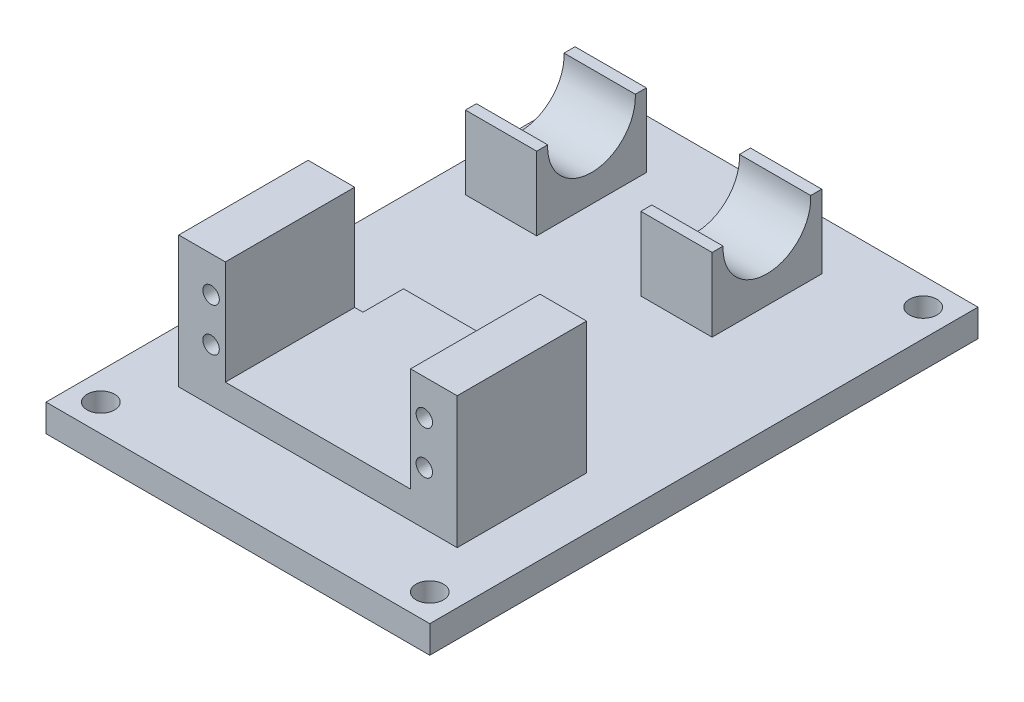
SolidWorks part; units mm, degrees
ref_plane "Front" through (0, 0, 0) normal (0, 0, 1) x (1, 0, 0)
ref_plane "Top" through (0, 0, 0) normal (0, 1, 0) x (1, 0, 0)
ref_plane "Right" through (0, 0, 0) normal (1, 0, 0) x (0, 0, -1)
sketch "Sketch1" plane through (0, 0, 0) normal (0, 1, 0) x (1, 0, 0)
  line L1 (-35, -50) -> (35, -50)
  line L2 (-35, -50) -> (-35, 50)
  line L3 (-35, 50) -> (35, 50)
  line L4 (35, -50) -> (35, 50)
  line L5 (-35, -50) -> (35, 50) construction
  line L6 (-35, 50) -> (35, -50) construction
  point P0 (0, 0)
  dimension "D1" = 70
  dimension "D2" = 100
extrude "Boss-Extrude1" add sketch "Sketch1" along normal blind 5
sketch "Sketch2" plane through (0, 5, 0) normal (0, 1, 0) x (1, 0, 0)
  line L0 (0, 49.7148) -> (0, -60.7462) construction
  line L1 (-15.2897, -11.9) -> (-25.2897, -11.9)
  line L2 (-35, 31) -> (35, 31) construction
  line L3 (-7, 50) -> (-7, -50) construction
  line L4 (-15.2897, -4.5) -> (15.5, -4.5)
  line L5 (-35, -50) -> (35, -50) construction
  line L6 (-35, 50) -> (-35, -50) construction
  line L7 (35, 50) -> (-35, 50) construction
  line L8 (35, -50) -> (35, 50) construction
  line L9 (-29.5, 21) -> (-16.5, 21)
  line L10 (15.5, 41) -> (2.5, 21) construction
  line L11 (15.5, 21) -> (2.5, 41) construction
  line L12 (-29.5, 21) -> (-29.5, 41)
  line L13 (-29.5, 41) -> (-16.5, 41)
  line L14 (-25.2897, -11.9) -> (-25.2897, -35.5)
  line L15 (-16.5, 21) -> (-16.5, 41)
  line L16 (-15.2897, -11.9) -> (-15.2897, -4.5)
  line L17 (15.5, -4.5) -> (15.5, -11.9)
  line L18 (15.5, -11.9) -> (25.5, -11.9)
  line L19 (25.5, -11.9) -> (25.5, -35.5)
  line L20 (25.5, -35.5) -> (-25.2897, -35.5)
  line L21 (-29.5, 21) -> (-16.5, 41) construction
  line L22 (-29.5, 41) -> (-16.5, 21) construction
  line L23 (2.5, 21) -> (2.5, 41)
  line L24 (15.5, 41) -> (2.5, 41)
  line L25 (15.5, 21) -> (15.5, 41)
  line L26 (15.5, 21) -> (2.5, 21)
  point P0 (0, -20)
  point P10 (-23, 31)
  point P33 (9, 31)
  dimension "D1" = 10
  dimension "D2" = 13
  dimension "D3" = 10
  dimension "D4" = 20
  dimension "D5" = 23
  dimension "D6" = 19
  dimension "D7" = 7.4
  dimension "D8" = 7
extrude "Boss-Extrude2" add sketch "Sketch2" along normal blind 5
sketch "Sketch4" plane through (0, 10, 0) normal (0, 1, 0) x (1, 0, 0)
  line L0 (-25.2897, -11.9) -> (-16.7897, -11.9)
  line L1 (-15.2897, -11.9) -> (-25.2897, -11.9) construction
  line L2 (-16.7897, -11.9) -> (-16.7897, -35.5)
  line L3 (-25.2897, -35.5) -> (25.5, -35.5) construction
  line L4 (-16.7897, -35.5) -> (-25.2897, -35.5)
  line L5 (-25.2897, -35.5) -> (-25.2897, -11.9)
  line L6 (25.5, -11.9) -> (17, -11.9)
  line L7 (25.5, -11.9) -> (15.5, -11.9) construction
  line L8 (17, -11.9) -> (17, -35.5)
  line L9 (-25.2897, -35.5) -> (25.5, -35.5) construction
  line L10 (17, -35.5) -> (25.5, -35.5)
  line L11 (25.5, -35.5) -> (25.5, -11.9)
  dimension "D1" = 8.5
  dimension "D2" = 8.5
extrude "Boss-Extrude3" add sketch "Sketch4" along normal blind 19
sketch "Sketch5" plane through (0, 0, 11.9) normal (0, 0, -1) x (-1, 0, 0)
  line L1 (16.7897, 29) -> (25.2897, 29) construction
  line L4 (-17, 29) -> (-17, 10) construction
  circle A0 centre (19.39, 22.5) radius 1.5
  circle A1 centre (19.39, 14.63) radius 1.5
  circle A2 centre (-19.5, 22.5) radius 1.5
  circle A3 centre (-19.5, 14.63) radius 1.5
  point P16 (-17, 27.3801)
  dimension "D1" = 3
  dimension "D5" = 3
  dimension "D8" = 3
  dimension "D9" = 3
  dimension "D10" = 2.5
  dimension "D2" = 38.89
  dimension "D3" = 6.5
  dimension "D4" = 7.87
  dimension "D7" = 2.5
extrude "Cut-Extrude1" cut sketch "Sketch5" against normal blind 26
sketch "Sketch6" plane through (0, 10, 0) normal (0, 1, 0) x (1, 0, 0)
  line L1 (-29.5, 21) -> (-16.5, 21)
  line L2 (-29.5, 21) -> (-29.5, 41)
  line L3 (-29.5, 41) -> (-16.5, 41)
  line L4 (-16.5, 21) -> (-16.5, 41)
  line L5 (2.5, 21) -> (15.5, 21)
  line L6 (2.5, 21) -> (2.5, 41)
  line L7 (2.5, 41) -> (15.5, 41)
  line L8 (15.5, 21) -> (15.5, 41)
extrude "Boss-Extrude4" add sketch "Sketch6" along normal blind 8.385
sketch "Sketch7" plane through (-29.5, 0, 0) normal (-1, 0, 0) x (0, 0, 1)
  line L0 (-50, 5) -> (50, 5) construction
  line L1 (-21, 18.385) -> (-21, 5) construction
  circle A0 centre (-31, 18) radius 8
  dimension "D1" = 16
  dimension "D2" = 13
  dimension "D3" = 10
extrude "Cut-Extrude2" cut sketch "Sketch7" against normal blind 63
sketch "Sketch8" plane through (0, 5, 0) normal (0, 1, 0) x (1, 0, 0)
  line L0 (30, 60.0505) -> (30, -64.775) construction
  line L1 (49.616, 45) -> (-58.6187, 45) construction
  line L2 (35, -50) -> (35, 50) construction
  line L3 (35, 50) -> (-35, 50) construction
  line L4 (-30, 54.0926) -> (-30, -67.0737) construction
  line L5 (47.4701, -45) -> (-63.2625, -45) construction
  line L6 (-35, -50) -> (35, -50) construction
  line L7 (-35, 50) -> (-35, -50) construction
  circle A0 centre (30, 45) radius 2.5
  circle A1 centre (-30, 45) radius 2.5
  circle A2 centre (-30, -45) radius 2.5
  circle A3 centre (30, -45) radius 2.5
  dimension "D3" = 5
  dimension "D6" = 5
  dimension "D7" = 5
  dimension "D8" = 5
  dimension "D1" = 5
  dimension "D2" = 5
  dimension "D4" = 5
  dimension "D5" = 5
extrude "Cut-Extrude3" cut sketch "Sketch8" against normal up to next
